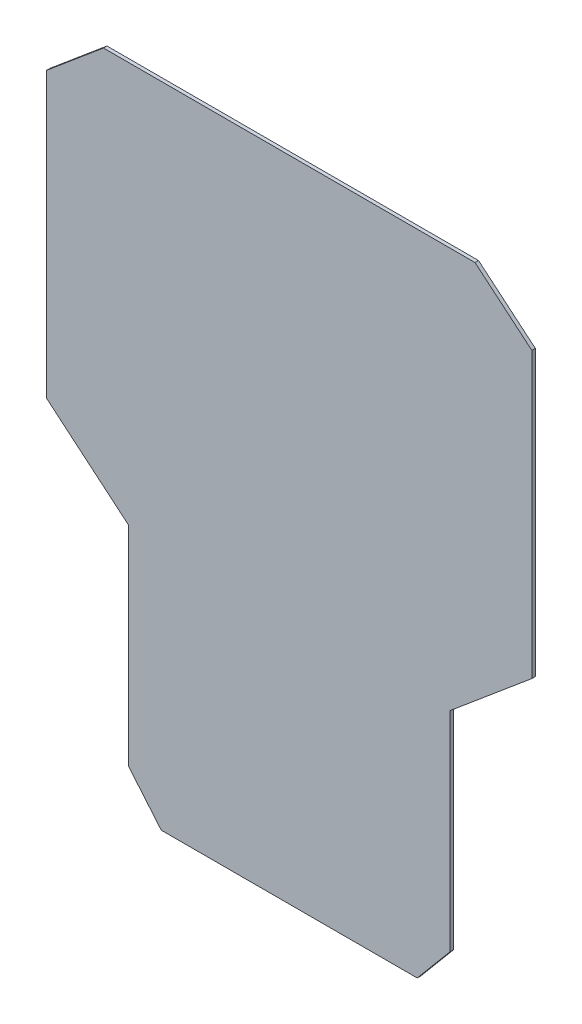
SolidWorks part; units mm, degrees
ref_plane "Plano frontal" through (0, 0, 0) normal (0, 0, 1) x (1, 0, 0)
ref_plane "Plano superior" through (0, 0, 0) normal (0, 1, 0) x (1, 0, 0)
ref_plane "Plano direito" through (0, 0, 0) normal (1, 0, 0) x (0, 0, -1)
sketch "Esboço1" plane through (0, 0, 0) normal (0, 0, 1) x (1, 0, 0)
  line L4 (0, -175.0296) -> (0, 175.0296) construction
  line L7 (-69, -140.4097) -> (-54.8706, -157.2485)
  line L8 (-54.8706, -157.2485) -> (54.8706, -157.2485)
  line L11 (-104, 100.3077) -> (-79.636, 120.7515)
  line L12 (-104, 100.3077) -> (-104, -21.5245)
  line L13 (-104, -21.5245) -> (-69, -50.893)
  line L14 (-69, -50.893) -> (-69, -140.4097)
  line L15 (54.8706, -157.2485) -> (69, -140.4097)
  line L17 (-79.636, 120.7515) -> (79.636, 120.7515)
  line L18 (69, -50.893) -> (69, -140.4097)
  line L19 (104, -21.5245) -> (69, -50.893)
  line L20 (104, 100.3077) -> (104, -21.5245)
  line L24 (79.636, 120.7515) -> (104, 100.3077)
extrude "Ressalto-extrusão1" add sketch "Esboço1" along normal blind 1.5
